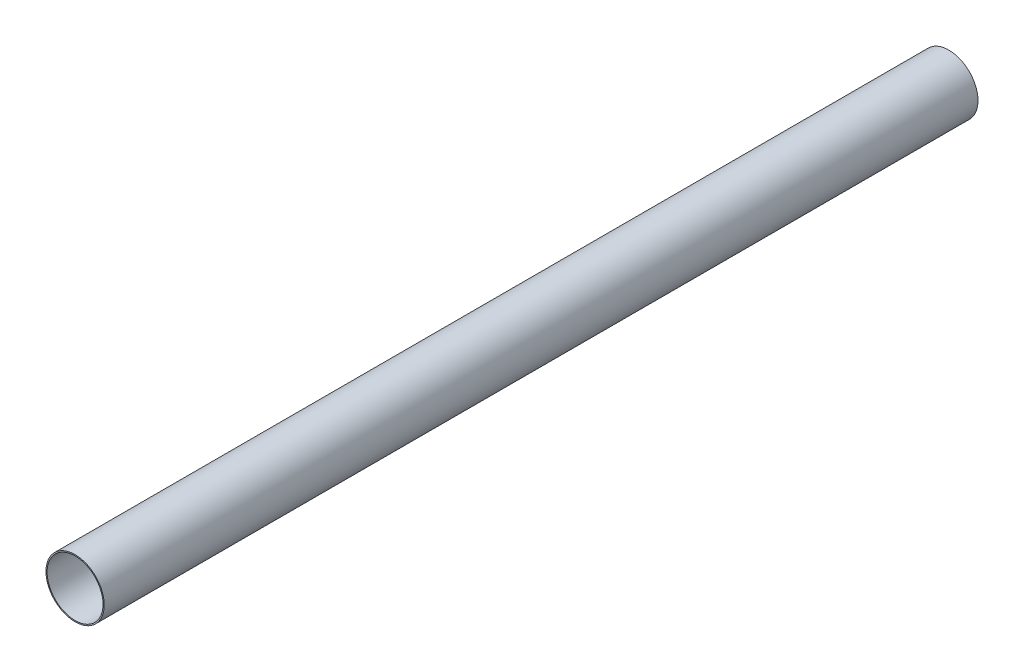
SolidWorks part; units mm, degrees
material "E-Glass Fiber"
ref_plane "Front Plane" through (0, 0, 0) normal (0, 0, 1) x (1, 0, 0)
ref_plane "Top Plane" through (0, 0, 0) normal (0, 1, 0) x (1, 0, 0)
ref_plane "Right Plane" through (0, 0, 0) normal (1, 0, 0) x (0, 0, -1)
sketch "Sketch1" plane through (0, 0, 0) normal (0, 0, 1) x (1, 0, 0)
  circle A0 centre (0, 0) radius 48.8061
  circle A1 centre (0, 0) radius 50.8
  dimension "D1" = 101.6
  dimension "D2" = 97.6122
extrude "Boss-Extrude1" add sketch "Sketch1" along normal blind 1524
